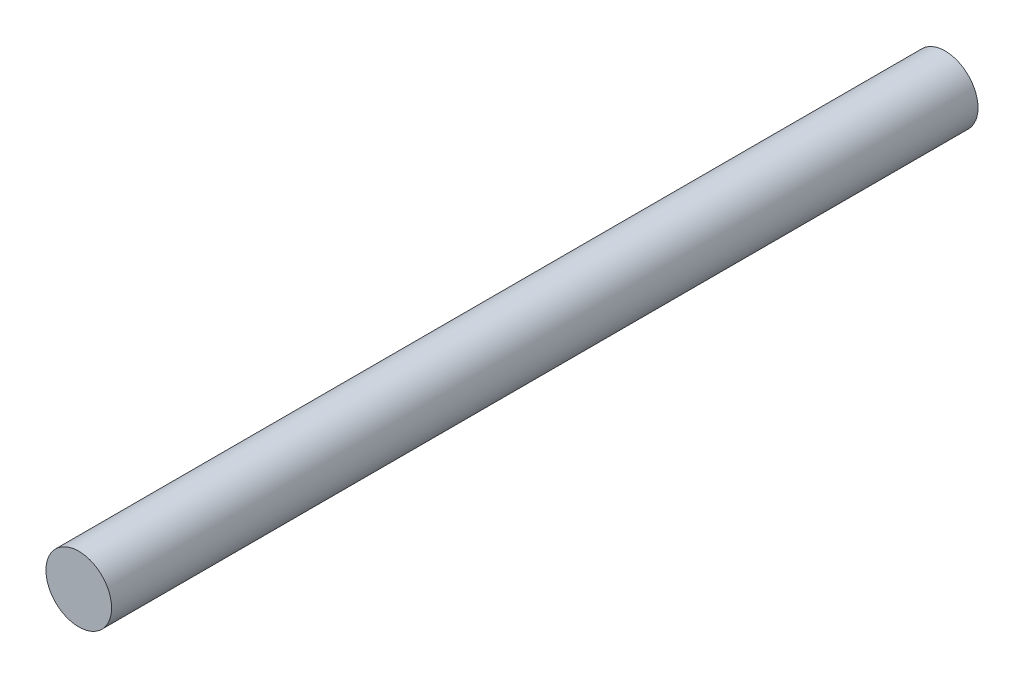
SolidWorks part; units mm, degrees
material "AISI 1020"
ref_plane "Alzado" through (0, 0, 0) normal (0, 0, 1) x (1, 0, 0)
ref_plane "Planta" through (0, 0, 0) normal (0, 1, 0) x (1, 0, 0)
ref_plane "Vista lateral" through (0, 0, 0) normal (1, 0, 0) x (0, 0, -1)
sketch "Croquis1" plane through (0, 0, 0) normal (0, 0, 1) x (1, 0, 0)
  circle A0 centre (0, 0) radius 2.5
  dimension "D1" = 5
extrude "Saliente-Extruir1" add sketch "Croquis1" along normal blind 66
